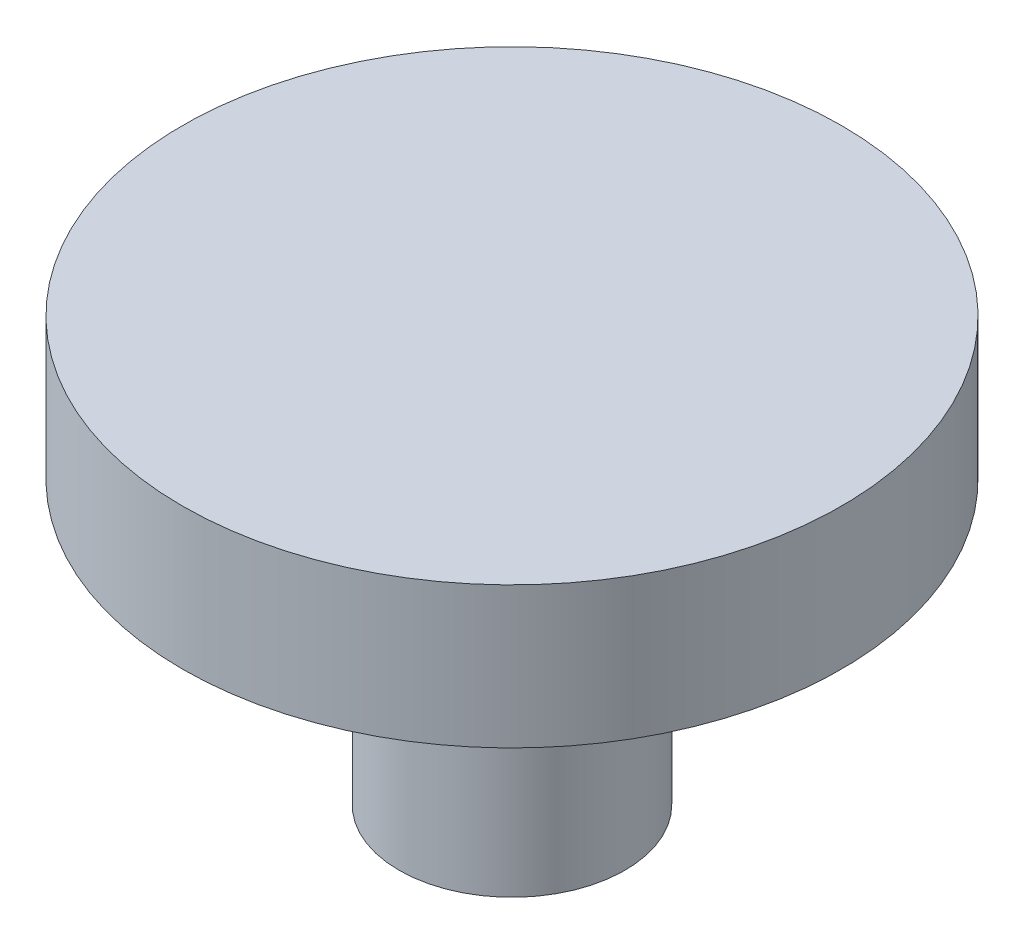
SolidWorks part; units mm, degrees
ref_plane "Alzado" through (0, 0, 0) normal (0, 0, 1) x (1, 0, 0)
ref_plane "Planta" through (0, 0, 0) normal (0, 1, 0) x (1, 0, 0)
ref_plane "Vista lateral" through (0, 0, 0) normal (1, 0, 0) x (0, 0, -1)
sketch "Croquis1" plane through (0, 0, 0) normal (0, 1, 0) x (1, 0, 0)
  line L0 (0, 51.8966) -> (0, -80.3044) construction
  line L1 (-89.12, 0) -> (132.6366, 0) construction
  circle A0 centre (0, 0) radius 2.4
  dimension "D2" = 4.8
  dimension "D1" = 0
extrude "Saliente-Extruir1" add sketch "Croquis1" along normal mid plane 6
sketch "Croquis2" plane through (0, 3, 0) normal (0, 1, 0) x (1, 0, 0)
  circle A0 centre (0, 0) radius 7
  dimension "D1" = 14
  dimension "D2" = 0
extrude "Saliente-Extruir2" add sketch "Croquis2" along normal blind 3
